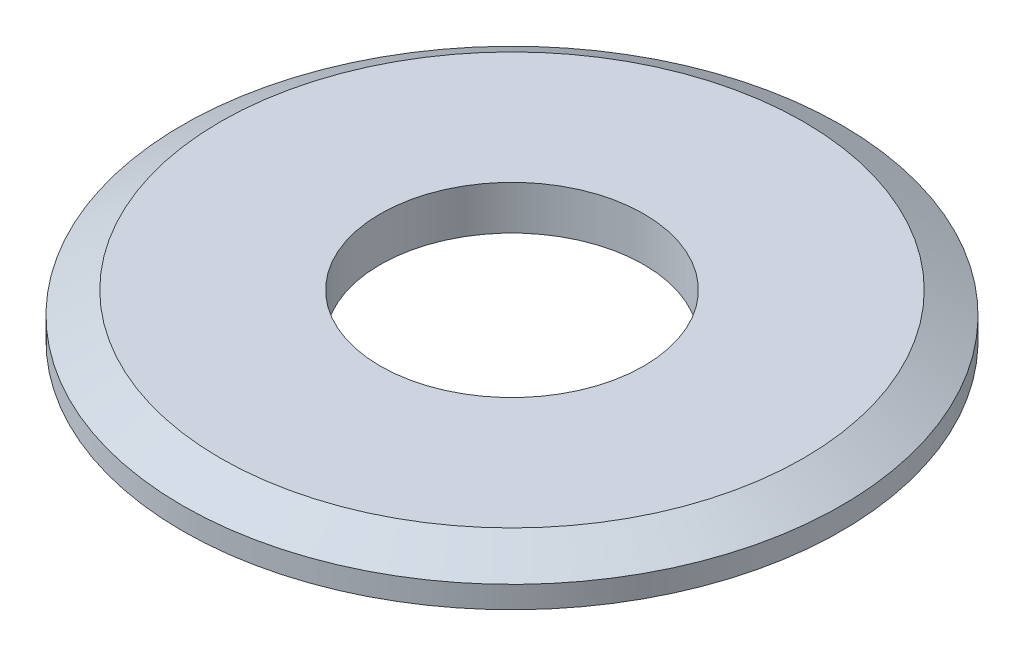
SolidWorks part; units mm, degrees
ref_plane "Front Plane" through (0, 0, 0) normal (0, 0, 1) x (1, 0, 0)
ref_plane "Top Plane" through (0, 0, 0) normal (0, 1, 0) x (1, 0, 0)
ref_plane "Right Plane" through (0, 0, 0) normal (1, 0, 0) x (0, 0, -1)
sketch "Sketch1" plane through (0, 0, 0) normal (0, 1, 0) x (1, 0, 0)
  circle A0 centre (0, 0) radius 7.5
  dimension "D1" = 15
extrude "Boss-Extrude1" add sketch "Sketch1" along normal blind 1 contours A0
chamfer "Chamfer1" distance 0.5 angle 60 1 edges at (0, 1, 7.5)
sketch "Sketch2" plane through (0, 1, 0) normal (0, 1, 0) x (1, 0, 0)
  circle A0 centre (0, 0) radius 3
  dimension "D1" = 6
extrude "Cut-Extrude1" cut sketch "Sketch2" against normal blind 1
